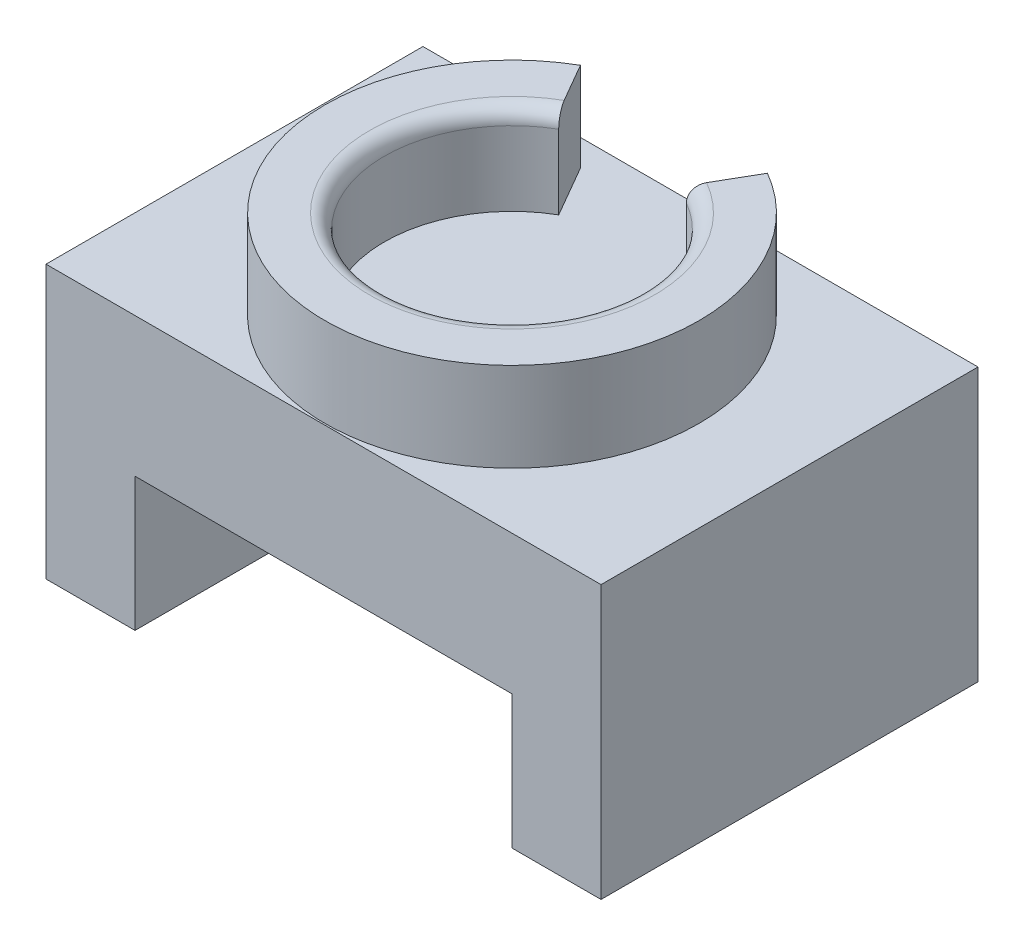
SolidWorks part; units mm, degrees
ref_plane "Front Plane" through (0, 0, 0) normal (0, 0, 1) x (1, 0, 0)
ref_plane "Top Plane" through (0, 0, 0) normal (0, 1, 0) x (1, 0, 0)
ref_plane "Right Plane" through (0, 0, 0) normal (1, 0, 0) x (0, 0, -1)
sketch "Sketch1" plane through (0, 0, 0) normal (0, 0, 1) x (1, 0, 0)
  line L0 (-10.1895, 0) -> (-10.1895, 9)
  line L1 (-10.1895, 9) -> (15.2105, 9)
  line L2 (15.2105, 9) -> (15.2105, 0)
  line L3 (15.2105, 0) -> (21.2105, 0)
  line L4 (21.2105, 0) -> (21.2105, 18.375)
  line L5 (21.2105, 18.375) -> (-16.1895, 18.375)
  line L6 (-16.1895, 18.375) -> (-16.1895, 0)
  line L7 (-16.1895, 0) -> (-10.1895, 0)
  dimension "D1" = 25.4
  dimension "D2" = 9
  dimension "D3" = 18.375
  dimension "D4" = 6
  dimension "D5" = 6
extrude "Boss-Extrude1" add sketch "Sketch1" along normal blind 25.4
sketch "Sketch2" plane through (0, 18.375, 0) normal (0, 1, 0) x (1, 0, 0)
  line L0 (2.5105, -25.4) -> (2.5105, 0) construction
  line L1 (21.2105, -25.4) -> (-16.1895, -25.4) construction
  line L2 (21.2105, 0) -> (-16.1895, 0) construction
  circle A0 centre (2.5105, -12.7) radius 8.6
  circle A1 centre (2.5105, -12.7) radius 12.6
  dimension "D1" = 17.2
  dimension "D2" = 4
extrude "Boss-Extrude2" add sketch "Sketch2" along normal blind 6
sketch "Sketch3" plane through (0, 24.375, 0) normal (0, 1, 0) x (1, 0, 0)
  line L0 (2.5105, -12.7) -> (2.5105, -0.1)
  line L1 (2.5105, -12.7) -> (8.8105, -1.7881)
  line L2 (2.5105, -12.7) -> (-3.7895, -1.7881)
  circle A1 centre (2.5105, -12.7) radius 12.6
  circle A2 centre (2.5105, -12.7) radius 12.6
  circle M5 centre (2.5105, -12.7) radius 12.6
  circle M6 centre (2.5105, -12.7) radius 8.6
  dimension "D2" = 30
  dimension "D3" = 30
  dimension "D1" = 0
extrude "Cut-Extrude1" cut sketch "Sketch3" against normal blind 6 contours L2 L0 M6 M5 | L1 L0 M6 M5
fillet "Fillet1" radius 1 1 edges at (2.5105, 24.375, 21.3)
